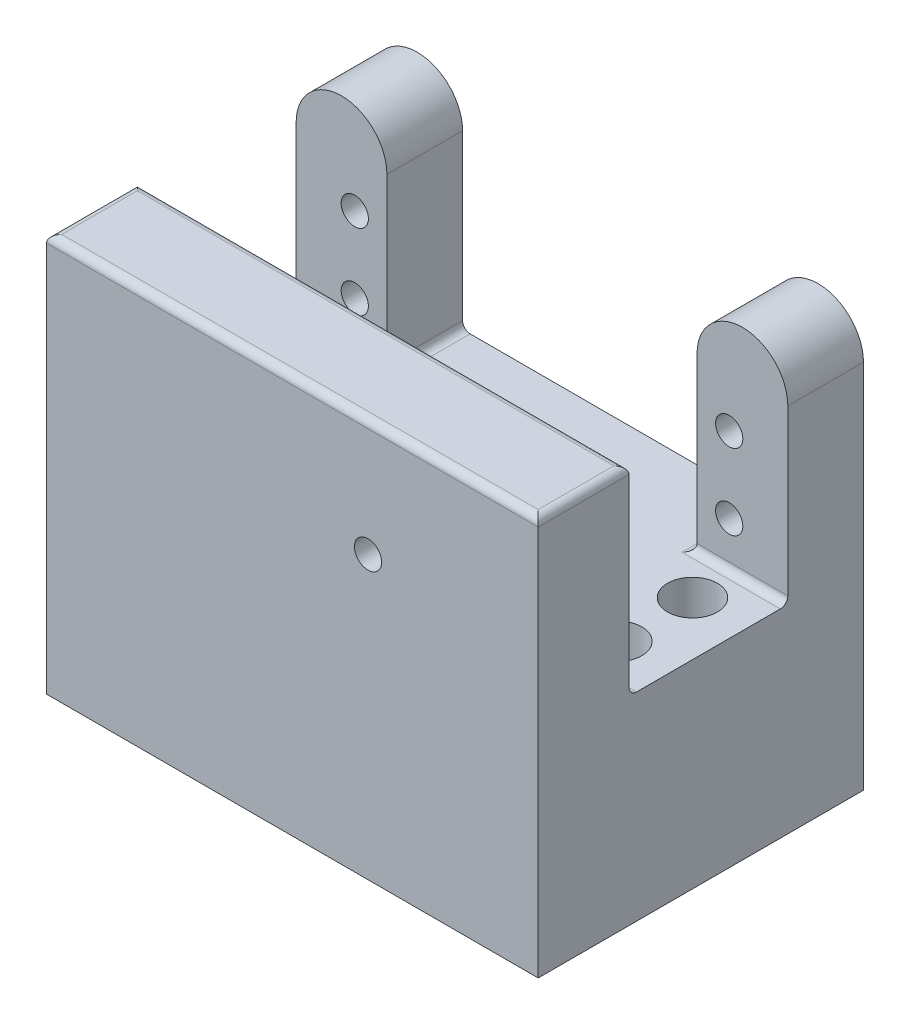
SolidWorks part; units mm, degrees
ref_plane "Front Plane" through (0, 0, 0) normal (0, 0, 1) x (1, 0, 0)
ref_plane "Top Plane" through (0, 0, 0) normal (0, 1, 0) x (1, 0, 0)
ref_plane "Right Plane" through (0, 0, 0) normal (1, 0, 0) x (0, 0, -1)
sketch "Sketch1" plane through (0, 0, 0) normal (0, 0, 1) x (1, 0, 0)
  line L0 (0, 25.9884) -> (0, -27.0349) construction
  line L1 (-6, 14.3023) -> (-6, -20.6977)
  line L2 (6, 14.3023) -> (6, -20.6977)
  line L3 (-6, -20.6977) -> (6, -20.6977)
  arc A0 (-6, 14.3023) -> (6, 14.3023) centre (0, 14.3023) cw
  dimension "D1" = 35
  dimension "D2" = 12
extrude "Boss-Extrude1" add sketch "Sketch1" along normal blind 10
sketch "Sketch2" plane through (0, 0, 10) normal (0, 0, 1) x (1, 0, 0)
  line L0 (6, -20.6977) -> (6, 14.3023) construction
  line L1 (-6, -20.6977) -> (6, -20.6977)
  line L2 (-6, -20.6977) -> (-6, -8.4477)
  line L3 (-6, -8.4477) -> (6, -8.4477)
  line L4 (6, -20.6977) -> (6, -8.4477)
  dimension "D1" = 12.25
extrude "Boss-Extrude2" add sketch "Sketch2" along normal blind 21 contours L3 L4 L1 L2
sketch "Sketch4" plane through (0, 0, 31) normal (0, 0, 1) x (1, 0, 0)
  line L1 (6, -20.6977) -> (-59, -20.6977)
  line L2 (6, -20.6977) -> (6, 17.9393)
  line L3 (6, 17.9393) -> (-59, 17.9393)
  line L4 (-59, -20.6977) -> (-59, 17.9393)
  dimension "D1" = 65
extrude "Boss-Extrude3" add sketch "Sketch4" along normal blind 12
ref_plane "Plane1" through (-26.5, 0, 0) normal (-1, 0, 0) x (0, 0, 1)
sketch "Sketch11" plane through (0, 0, 0) normal (0, 0, -1) x (-1, 0, 0)
  circle A0 centre (51.25, 8) radius 1.5
  circle A1 centre (51.25, -2) radius 1.5
  circle A3 centre (1.75, 7.5522) radius 1.5
  circle A4 centre (1.75, -2.4478) radius 1.5
  dimension "D1" = 49.5
  dimension "D4" = 3
  dimension "D5" = 3
  dimension "D6" = 3
  dimension "D7" = 3
  dimension "D2" = 10
  dimension "D3" = 49.5
  dimension "D8" = 10
mirror "Mirror2" about plane through (-26.5, 0, 0) normal (-1, 0, 0) of "Boss-Extrude2"
mirror "Mirror3" about plane through (-26.5, 0, 0) normal (-1, 0, 0) of "Boss-Extrude1"
hole_wizard "Ø3.6 (3.6) Diameter Hole1" positions "Sketch14" profile "Sketch15" hole size "Ø3.6" standard "ANSI Metric"
sketch "Sketch14" plane through (0, 0, 0) normal (0, 0, -1) x (-1, 0, 0)
  point P0 (1.75, 7.5522)
  point P3 (1.75, -2.4478)
  point P6 (51.25, 8)
  point P9 (51.25, -2)
sketch "Sketch15" plane through (-1.75, 7.5522, 0) normal (1, 0, 0) x (0, 1, 0)
  line L0 (0, 0) -> (0, 11.0815)
  line L1 (0, 11.0815) -> (1.8, 10)
  line L2 (1.8, 10) -> (1.8, 0)
  line L5 (1.8, 0) -> (0, 0)
  line L10 (0, 11.0815) -> (-1.8, 10) construction
  line L11 (0, -6.35) -> (0, 107.95) construction
  dimension "Hole Dia." = 3.6
  dimension "Hole Depth" = 10
  dimension "Drill Angle" = 118
sketch "Sketch21" plane through (0, 0, 31) normal (0, 0, -1) x (-1, 0, 0)
  line L1 (6, -8.4477) -> (47, -8.4477)
  line L2 (6, -8.4477) -> (6, -20.6977)
  line L3 (6, -20.6977) -> (47, -20.6977)
  line L4 (47, -8.4477) -> (47, -20.6977)
extrude "Boss-Extrude4" add sketch "Sketch21" along normal up to surface (31 mm away) up to face at (-3.55, 7.5522, 0)
sketch "Sketch23" plane through (0, -20.6977, 0) normal (0, -1, 0) x (1, 0, 0)
  line L1 (-59, 43) -> (6, 43)
  line L2 (-59, 43) -> (-59, 0)
  line L3 (-59, 0) -> (6, 0)
  line L4 (6, 43) -> (6, 0)
extrude "Boss-Extrude6" add sketch "Sketch23" along normal blind 14
sketch "Sketch24" plane through (0, -34.6977, 0) normal (0, -1, 0) x (-1, 0, 0)
  line L6 (-6, 0) -> (-6, -43) construction
  circle A0 centre (1.1, -25.5) radius 3
  circle A2 centre (51.9, -25.5) radius 3
  circle A4 centre (1.1, -15.5) radius 3
  circle A5 centre (51.9, -15.5) radius 3
  dimension "D4" = 6
  dimension "D5" = 6
  dimension "D1" = 10
  dimension "D2" = 10
  dimension "D8" = 7.1
fillet "Fillet1" radius 1 9 edges at (-26.5, 17.9393, 43) (-26.5, 17.9393, 31) (6, 17.9393, 37) (-59, 17.9393, 37) (-53, -8.4477, 10) (0, -8.4477, 10) (-6, -8.4477, 5) (-47, -8.4477, 5) (-26.5, -8.4477, 31)
hole_wizard "Ø6.6 (6.6) Diameter Hole1" positions "Sketch25" profile "Sketch26" hole size "Ø6.6" standard "ANSI Metric" end condition through all
sketch "Sketch25" plane through (0, -34.6977, 0) normal (0, -1, 0) x (-1, 0, 0)
  point P0 (1.1, -15.5)
  point P3 (1.1, -25.5)
  point P6 (51.9, -15.5)
  point P9 (51.9, -25.5)
sketch "Sketch26" plane through (-1.1, -34.6977, 15.5) normal (1, 0, 0) x (0, 0, -1)
  line L0 (0, 0) -> (0, 55)
  line L1 (0, 55) -> (3.3, 55)
  line L2 (3.3, 55) -> (3.3, 0)
  line L5 (3.3, 0) -> (0, 0)
  line L11 (0, -6.35) -> (0, 107.95) construction
  dimension "Thru Hole Dia." = 6.6
  dimension "Thru Hole Depth" = 55
sketch "Sketch28" plane through (0, 0, 43) normal (0, 0, 1) x (1, 0, 0)
  circle A2 centre (-16.5, 2.553) radius 1.8
extrude "Cut-Extrude1" cut sketch "Sketch28" against normal through all
